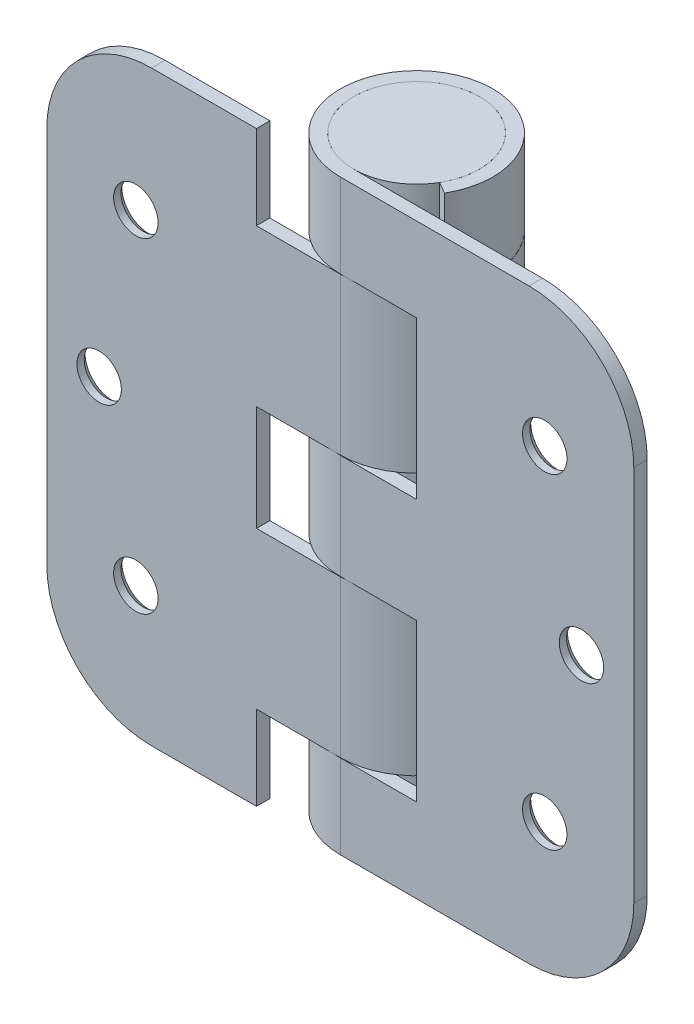
SolidWorks part; units mm, degrees
material "Nickel"
ref_plane "Front" through (0, 0, 0) normal (0, 0, 1) x (1, 0, 0)
ref_plane "Top" through (0, 0, 0) normal (0, 1, 0) x (1, 0, 0)
ref_plane "Right" through (0, 0, 0) normal (1, 0, 0) x (0, 0, -1)
sketch "Sketch1" plane through (0, 0, 0) normal (0, 1, 0) x (1, 0, 0)
  line L0 (0, 0) -> (10.0087, -5.7785) construction
  line L1 (0, -9.525) -> (44.45, -9.525)
  line L2 (8.2489, -4.7625) -> (10.0087, -5.7785)
  line L3 (0, -11.557) -> (44.45, -11.557)
  line L4 (44.45, -9.525) -> (44.45, -11.557)
  arc A0 (8.2489, -4.7625) -> (0, -9.525) centre (0, 0) ccw
  arc A1 (10.0087, -5.7785) -> (0, -11.557) centre (0, 0) ccw
  dimension "D2" = 44.45
  dimension "D3" = 19.05
  dimension "D1" = 30
  dimension "D4" = 2.032
extrude "Extrude1" add sketch "Sketch1" along normal mid plane 88.9
sketch "Sketch2" plane through (0, 0, 9.525) normal (0, 0, -1) x (-1, 0, 0)
  line L0 (11.557, 44.45) -> (11.557, 31.75)
  line L1 (11.557, 31.75) -> (-11.557, 31.75)
  line L2 (-11.557, 31.75) -> (-11.557, 7.9375)
  line L3 (-11.557, 7.9375) -> (11.557, 7.9375)
  line L4 (11.557, 7.9375) -> (11.557, -7.9375)
  line L5 (11.557, -7.9375) -> (-11.557, -7.9375)
  line L6 (-11.557, -7.9375) -> (-11.557, -31.75)
  line L7 (-11.557, -31.75) -> (11.557, -31.75)
  line L8 (11.557, -31.75) -> (11.557, -44.45)
  line L9 (-44.45, -44.45) -> (0, -44.45) construction
  line L10 (-44.45, 44.45) -> (0, 44.45) construction
  line L11 (11.557, -44.45) -> (11.557, 44.45) construction
  line L12 (-11.557, 44.45) -> (-11.557, -44.45) construction
  point P15 (11.557, 0)
  point P20 (-11.557, 19.8438)
  point P21 (-11.557, -19.8438)
  dimension "D1" = 15.875
  dimension "D2" = 12.7
extrude "Cut-Extrude1" cut sketch "Sketch2" against normal through all and the other way through all
ref_plane "Plane1" through (0, 19.8438, 0) normal (0, 1, 0) x (-1, 0, 0)
sketch "Sketch3" plane through (0, 19.8438, 0) normal (0, 1, 0) x (-1, 0, 0)
  line L0 (0, 6.7888) -> (0, -8.653) construction
  line L1 (44.45, 11.557) -> (44.45, 9.525)
  line L2 (8.2489, 4.7625) -> (10.0087, 5.7785)
  line L3 (0, 9.525) -> (44.45, 9.525)
  line L4 (-8.2489, 4.7625) -> (-10.0087, 5.7785)
  line L5 (0, 11.557) -> (-44.45, 11.557)
  line L6 (-44.45, 11.557) -> (-44.45, 9.525)
  line L7 (-44.45, 9.525) -> (0, 9.525)
  line L9 (44.45, 11.557) -> (0, 11.557)
  arc A2 (-8.2489, 4.7625) -> (0, 9.525) centre (0, 0) ccw
  arc A3 (-10.0087, 5.7785) -> (0, 11.557) centre (0, 0) ccw
  arc A4 (0, 9.525) -> (8.2489, 4.7625) centre (0, 0) ccw
  arc A5 (0, 11.557) -> (10.0087, 5.7785) centre (0, 0) ccw
  dimension "D1" = 0
extrude "Extrude2" add sketch "Sketch3" along normal offset from surface 0.0508 and the other way offset from surface (11.8554 mm away) 0.0508 up to face at (3.617, 31.75, 3.106) other way up to face at (3.617, 7.9375, 3.106)
ref_plane "Plane2" through (0, -19.8438, 0) normal (0, 1, 0) x (-1, 0, 0)
sketch "Sketch4" plane through (0, -19.8438, 0) normal (0, 1, 0) x (-1, 0, 0)
  line L4 (0, 9.525) -> (44.45, 9.525)
  line L5 (44.45, 9.525) -> (44.45, 11.557)
  line L6 (44.45, 11.557) -> (0, 11.557)
  line L7 (10.0087, 5.7785) -> (8.2489, 4.7625)
  line L8 (0, 9.525) -> (44.45, 9.525)
  line L9 (44.45, 9.525) -> (44.45, 11.557)
  line L10 (44.45, 11.557) -> (0, 11.557)
  line L11 (10.0087, 5.7785) -> (8.2489, 4.7625)
  arc A2 (0, 11.557) -> (10.0087, 5.7785) centre (0, 0) ccw
  arc A3 (0, 9.525) -> (8.2489, 4.7625) centre (0, 0) ccw
  arc A4 (0, 11.557) -> (10.0087, 5.7785) centre (0, 0) ccw
  arc A5 (0, 9.525) -> (8.2489, 4.7625) centre (0, 0) ccw
  dimension "D1" = 0
extrude "Extrude3" add sketch "Sketch4" along normal offset from surface 0.0508 and the other way offset from surface (11.8554 mm away) 0.0508 up to face at (3.617, -7.9375, 3.106) other way up to face at (3.617, -31.75, 3.106)
sketch "Sketch5" plane through (0, -19.8438, 0) normal (0, 1, 0) x (-1, 0, 0)
  line L0 (44.45, 9.525) -> (0, 9.525) construction
  line L1 (44.45, 11.557) -> (12.7, 11.557)
  line L2 (44.45, 11.557) -> (44.45, 9.525)
  line L3 (44.45, 9.525) -> (12.7, 9.525)
  line L4 (12.7, 11.557) -> (12.7, 9.525)
  dimension "D1" = 31.75
extrude "Extrude4" add sketch "Sketch5" along normal up to surface and the other way up to surface
sketch "Sketch6" plane through (0, 0, 0) normal (0, 0, 1) x (1, 0, 0)
  line L0 (0, 42.3616) -> (0, -43.1897) construction
  line L1 (-11.557, -44.45) -> (11.557, -44.45) construction
  line L2 (0, 44.45) -> (-9.525, 44.45)
  line L3 (0, 44.45) -> (0, -44.45)
  line L4 (0, -44.45) -> (-9.525, -44.45)
  line L5 (-9.525, 44.45) -> (-9.525, -44.45)
  dimension "D1" = 19.05
revolve "Revolve1" add sketch "Sketch6" angle 360 about L0
hole_wizard "CSK for #8 Flat Head Machine Screw2" positions "Sketch10" profile "Sketch9" countersink size "#8" standard "Ansi Inch"
sketch "Sketch10" plane through (0, 0, 9.525) normal (0, 0, -1) x (-1, 0, 0)
  line L0 (-8.3232, 0) -> (11.9672, 0) construction
  line L1 (44.45, 44.45) -> (44.45, -44.45) construction
  line L2 (0, 11.4703) -> (0, -6.6669) construction
  point P0 (36.5252, 0)
  point P4 (30.9626, 24.638)
  point P5 (30.9626, -24.638)
  point P10 (-30.9626, -24.638)
  point P11 (-36.5252, 0)
  point P12 (-30.9626, 24.638)
  dimension "D1" = 49.276
  dimension "D2" = 7.9248
  dimension "D3" = 5.5626
sketch "Sketch9" plane through (-36.5252, 0, 9.525) normal (1, 0, 0) x (0, 1, 0)
  line L0 (0, 0) -> (0, 4.1302)
  line L1 (0, 4.1302) -> (3.3655, 2.108)
  line L2 (3.3655, 2.108) -> (3.3655, 0.9204)
  line L3 (3.3655, 0.9204) -> (4.1656, 0)
  line L5 (4.1656, 0) -> (0, 0)
  line L6 (-3.3655, 0.9204) -> (-4.1656, 0) construction
  line L10 (0, 4.1302) -> (-3.3655, 2.108) construction
  line L11 (0, -6.35) -> (0, 107.95) construction
  dimension "Hole Dia." = 6.731
  dimension "Hole Depth" = 2.108
  dimension "Near C'Sink Dia." = 8.3312
  dimension "Near C'Sink Angle" = 82
  dimension "Drill Angle" = 118
sketch "Sketch11" plane through (0, 44.45, 0) normal (0, 1, 0) x (1, 0, 0)
  line L0 (0, 11.557) -> (0, 0) construction
  arc A0 (10.0087, -5.7785) -> (0, -11.557) centre (0, 0) ccw construction
  point P0 (0, 11.557)
ref_plane "Contact Plane1" through (0, 0, 11.557) normal (0, 0, 1) x (1, 0, 0)
fillet "Fillet1" radius 15.875 1 edges at (44.45, 44.45, 10.541)
fillet "Fillet2" radius 15.875 1 edges at (44.45, -44.45, 10.541)
fillet "Fillet3" radius 15.875 1 edges at (-44.45, 44.45, 10.541)
fillet "Fillet4" radius 15.875 1 edges at (-44.45, -44.45, 10.541)
